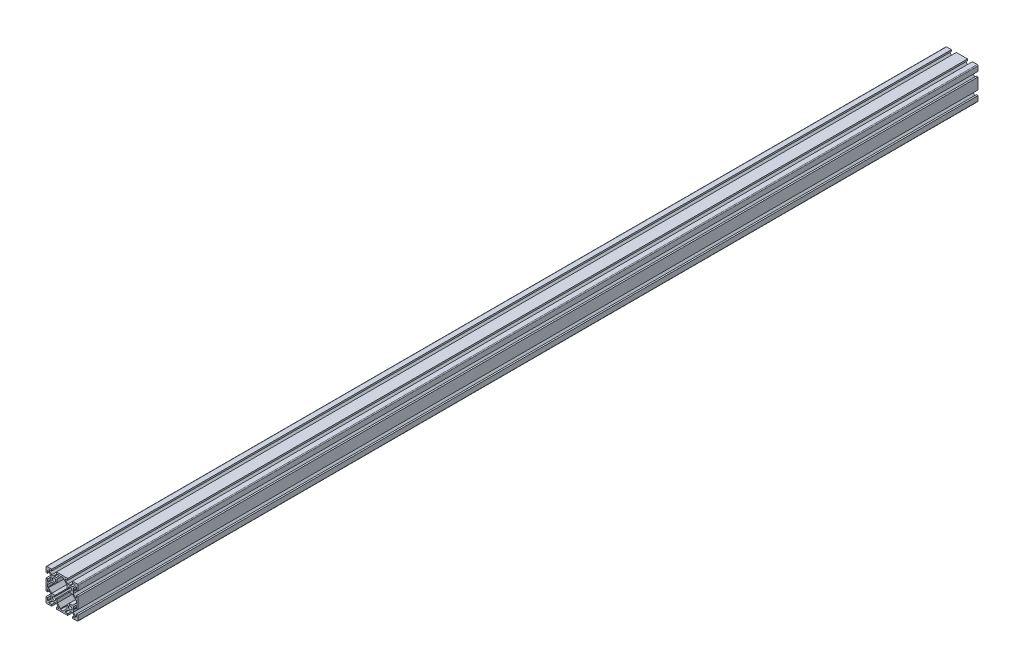
SolidWorks part; units mm, degrees
ref_plane "Front Plane" through (0, 0, 0) normal (0, 0, 1) x (1, 0, 0)
ref_plane "Top Plane" through (0, 0, 0) normal (0, 1, 0) x (1, 0, 0)
ref_plane "Right Plane" through (0, 0, 0) normal (1, 0, 0) x (0, 0, -1)
ref_plane "Plane1" through (0, 0, 0) normal (0, 0, 1) x (1, 0, 0)
sketch "Sketch1" plane through (0, 0, 0) normal (0, 0, 1) x (1, 0, 0)
  line L0 (-20, 13) -> (-18, 13)
  line L1 (-18, 13) -> (-18, 16)
  line L2 (-18, 16) -> (-17.0607, 16)
  line L3 (-17.0607, 16) -> (-14, 12.9393)
  line L4 (-14, 12.9393) -> (-14, 10.5196)
  line L5 (-14, 10.5196) -> (-13.7, 10)
  line L6 (-13.7, 10) -> (-14, 9.4804)
  line L7 (-14, 9.4804) -> (-14, 7.0607)
  line L8 (-14, 7.0607) -> (-17.0607, 4)
  line L9 (-17.0607, 4) -> (-18, 4)
  line L10 (-18, 4) -> (-18, 7)
  line L11 (-18, 7) -> (-20, 7)
  line L12 (-20, 7) -> (-20, -7)
  line L13 (-20, -7) -> (-18, -7)
  line L14 (-18, -7) -> (-18, -4)
  line L15 (-18, -4) -> (-17.0607, -4)
  line L16 (-17.0607, -4) -> (-14, -7.0607)
  line L17 (-14, -7.0607) -> (-14, -9.4804)
  line L18 (-14, -9.4804) -> (-13.7, -10)
  line L19 (-13.7, -10) -> (-14, -10.5196)
  line L20 (-14, -10.5196) -> (-14, -12.9393)
  line L21 (-14, -12.9393) -> (-17.0607, -16)
  line L22 (-17.0607, -16) -> (-18, -16)
  line L23 (-18, -16) -> (-18, -13)
  line L24 (-18, -13) -> (-20, -13)
  line L25 (-20, -13) -> (-20, -19)
  line L26 (-19, -20) -> (-13, -20)
  line L27 (-13, -20) -> (-13, -18)
  line L28 (-13, -18) -> (-16, -18)
  line L29 (-16, -18) -> (-16, -17.0607)
  line L30 (-16, -17.0607) -> (-12.9393, -14)
  line L31 (-12.9393, -14) -> (-10.5196, -14)
  line L32 (-10.5196, -14) -> (-10, -13.7)
  line L33 (-10, -13.7) -> (-9.4804, -14)
  line L34 (-9.4804, -14) -> (-7.0607, -14)
  line L35 (-7.0607, -14) -> (-4, -17.0607)
  line L36 (-4, -17.0607) -> (-4, -18)
  line L37 (-4, -18) -> (-7, -18)
  line L38 (-7, -18) -> (-7, -20)
  line L39 (-7, -20) -> (7, -20)
  line L40 (7, -20) -> (7, -18)
  line L41 (7, -18) -> (4, -18)
  line L42 (4, -18) -> (4, -17.0607)
  line L43 (4, -17.0607) -> (7.0607, -14)
  line L44 (7.0607, -14) -> (9.4804, -14)
  line L45 (9.4804, -14) -> (10, -13.7)
  line L46 (10, -13.7) -> (10.5196, -14)
  line L47 (10.5196, -14) -> (12.9393, -14)
  line L48 (12.9393, -14) -> (16, -17.0607)
  line L49 (16, -17.0607) -> (16, -18)
  line L50 (16, -18) -> (13, -18)
  line L51 (13, -18) -> (13, -20)
  line L52 (13, -20) -> (19, -20)
  line L53 (20, -19) -> (20, -13)
  line L54 (20, -13) -> (18, -13)
  line L55 (18, -13) -> (18, -16)
  line L56 (18, -16) -> (17.0607, -16)
  line L57 (17.0607, -16) -> (14, -12.9393)
  line L58 (14, -12.9393) -> (14, -10.5196)
  line L59 (14, -10.5196) -> (13.7, -10)
  line L60 (13.7, -10) -> (14, -9.4804)
  line L61 (14, -9.4804) -> (14, -7.0607)
  line L62 (14, -7.0607) -> (17.0607, -4)
  line L63 (17.0607, -4) -> (18, -4)
  line L64 (18, -4) -> (18, -7)
  line L65 (18, -7) -> (20, -7)
  line L66 (20, -7) -> (20, 7)
  line L67 (20, 7) -> (18, 7)
  line L68 (18, 7) -> (18, 4)
  line L69 (18, 4) -> (17.0607, 4)
  line L70 (17.0607, 4) -> (14, 7.0607)
  line L71 (14, 7.0607) -> (14, 9.4804)
  line L72 (14, 9.4804) -> (13.7, 10)
  line L73 (13.7, 10) -> (14, 10.5196)
  line L74 (14, 10.5196) -> (14, 12.9393)
  line L75 (14, 12.9393) -> (17.0607, 16)
  line L76 (17.0607, 16) -> (18, 16)
  line L77 (18, 16) -> (18, 13)
  line L78 (18, 13) -> (20, 13)
  line L79 (20, 13) -> (20, 19)
  line L80 (19, 20) -> (13, 20)
  line L81 (13, 20) -> (13, 18)
  line L82 (13, 18) -> (16, 18)
  line L83 (16, 18) -> (16, 17.0607)
  line L84 (16, 17.0607) -> (12.9393, 14)
  line L85 (12.9393, 14) -> (10.5196, 14)
  line L86 (10.5196, 14) -> (10, 13.7)
  line L87 (10, 13.7) -> (9.4804, 14)
  line L88 (9.4804, 14) -> (7.0607, 14)
  line L89 (7.0607, 14) -> (4, 17.0607)
  line L90 (4, 17.0607) -> (4, 18)
  line L91 (4, 18) -> (7, 18)
  line L92 (7, 18) -> (7, 20)
  line L93 (7, 20) -> (-7, 20)
  line L94 (-7, 20) -> (-7, 18)
  line L95 (-7, 18) -> (-4, 18)
  line L96 (-4, 18) -> (-4, 17.0607)
  line L97 (-4, 17.0607) -> (-7.0607, 14)
  line L98 (-7.0607, 14) -> (-9.4804, 14)
  line L99 (-9.4804, 14) -> (-10, 13.7)
  line L100 (-10, 13.7) -> (-10.5196, 14)
  line L101 (-10.5196, 14) -> (-12.9393, 14)
  line L102 (-12.9393, 14) -> (-16, 17.0607)
  line L103 (-16, 17.0607) -> (-16, 18)
  line L104 (-16, 18) -> (-13, 18)
  line L105 (-13, 18) -> (-13, 20)
  line L106 (-13, 20) -> (-19, 20)
  line L107 (-20, 19) -> (-20, 13)
  arc A0 (-20, -19) -> (-19, -20) centre (-19, -19) ccw
  arc A1 (19, -20) -> (20, -19) centre (19, -19) ccw
  arc A2 (20, 19) -> (19, 20) centre (19, 19) ccw
  arc A3 (-19, 20) -> (-20, 19) centre (-19, 19) ccw
extrude "Boss-Extrude1" add sketch "Sketch1" against normal blind 1120
ref_plane "Plane2" through (0, 0, 0) normal (0, 0, 1) x (1, 0, 0)
sketch "Sketch2" plane through (0, 0, 0) normal (0, 0, 1) x (1, 0, 0)
  line L0 (-18, 2) -> (-18, -2)
  line L1 (-18, -2) -> (-16.9393, -2)
  line L2 (-16.9393, -2) -> (-12.9393, -6)
  line L3 (-12.9393, -6) -> (-8.6667, -6)
  line L4 (-8.6667, -6) -> (-9.3359, -8.0078)
  line L5 (-8.0078, -9.3359) -> (-6, -8.6667)
  line L6 (-6, -8.6667) -> (-6, -12.9393)
  line L7 (-6, -12.9393) -> (-2, -16.9393)
  line L8 (-2, -16.9393) -> (-2, -18)
  line L9 (-2, -18) -> (2, -18)
  line L10 (2, -18) -> (2, -16.9393)
  line L11 (2, -16.9393) -> (6, -12.9393)
  line L12 (6, -12.9393) -> (6, -8.6667)
  line L13 (6, -8.6667) -> (8.0078, -9.3359)
  line L14 (9.3359, -8.0078) -> (8.6667, -6)
  line L15 (8.6667, -6) -> (12.9393, -6)
  line L16 (12.9393, -6) -> (16.9393, -2)
  line L17 (16.9393, -2) -> (18, -2)
  line L18 (18, -2) -> (18, 2)
  line L19 (18, 2) -> (16.9393, 2)
  line L20 (16.9393, 2) -> (12.9393, 6)
  line L21 (12.9393, 6) -> (8.6667, 6)
  line L22 (8.6667, 6) -> (9.3359, 8.0078)
  line L23 (8.0078, 9.3359) -> (6, 8.6667)
  line L24 (6, 8.6667) -> (6, 12.9393)
  line L25 (6, 12.9393) -> (2, 16.9393)
  line L26 (2, 16.9393) -> (2, 18)
  line L27 (2, 18) -> (-2, 18)
  line L28 (-2, 18) -> (-2, 16.9393)
  line L29 (-2, 16.9393) -> (-6, 12.9393)
  line L30 (-6, 12.9393) -> (-6, 8.6667)
  line L31 (-6, 8.6667) -> (-8.0078, 9.3359)
  line L32 (-9.3359, 8.0078) -> (-8.6667, 6)
  line L33 (-8.6667, 6) -> (-12.9393, 6)
  line L34 (-12.9393, 6) -> (-16.9393, 2)
  line L35 (-16.9393, 2) -> (-18, 2)
  arc A0 (-9.3359, -8.0078) -> (-8.0078, -9.3359) centre (-10, -10) ccw
  arc A1 (8.0078, -9.3359) -> (9.3359, -8.0078) centre (10, -10) ccw
  arc A2 (9.3359, 8.0078) -> (8.0078, 9.3359) centre (10, 10) ccw
  arc A3 (-8.0078, 9.3359) -> (-9.3359, 8.0078) centre (-10, 10) ccw
extrude "Cut-Extrude1" cut sketch "Sketch2" against normal blind 1182
